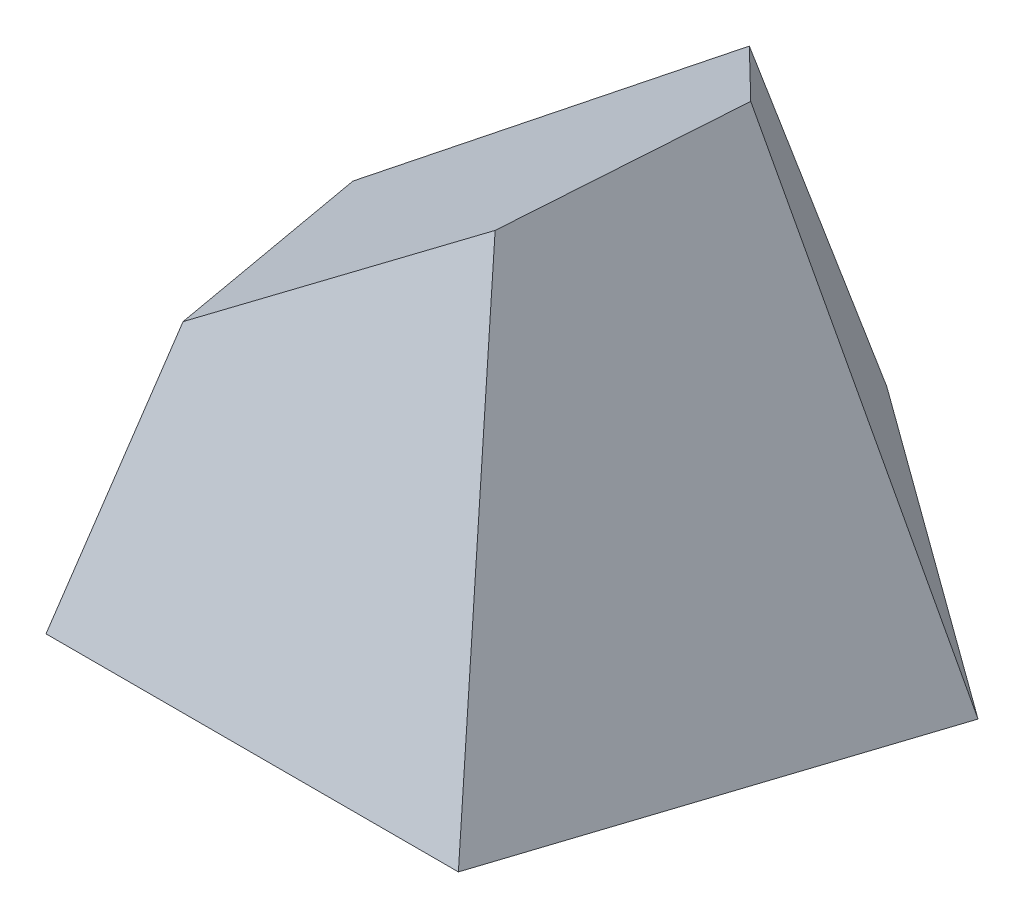
SolidWorks part; units mm, degrees
ref_plane "VP" through (0, 0, 0) normal (0, 0, 1) x (1, 0, 0)
ref_plane "HP" through (0, 0, 0) normal (0, 1, 0) x (1, 0, 0)
ref_plane "Right Plane" through (0, 0, 0) normal (1, 0, 0) x (0, 0, -1)
sketch "Sketch1" plane through (0, 0, 0) normal (0, 1, 0) x (1, 0, 0)
  line L1 (70.3607, -79.5537) -> (82.7214, -41.5114)
  line L2 (82.7214, -41.5114) -> (50.3607, -18)
  line L3 (50.3607, -18) -> (18, -41.5114)
  line L4 (18, -41.5114) -> (30.3607, -79.5537)
  line L5 (30.3607, -79.5537) -> (70.3607, -79.5537)
  circle A0 centre (50.3607, -52.026) radius 27.5276 construction
  dimension "D1" = 18
  dimension "D2" = 18
  dimension "D3" = 40
ref_plane "Plane1" through (0, 90, 0) normal (0, 1, 0) x (1, 0, 0)
sketch "Sketch2" plane through (0, 90, 0) normal (0, 1, 0) x (1, 0, 0)
  point P0 (50.3607, -52.026)
loft "Loft1" add profiles "Sketch2", "Sketch1"
sketch "Sketch3" plane through (0, 0, 0) normal (0, 1, 0) x (1, 0, 0)
  line L0 (0, 0) -> (0, -96.1937) construction
ref_plane "35 deg plane" through (0, 0, 0) normal (-0.5736, 0.8192, 0) x (0.8192, 0.5736, 0)
other "SurfaceCut1"
